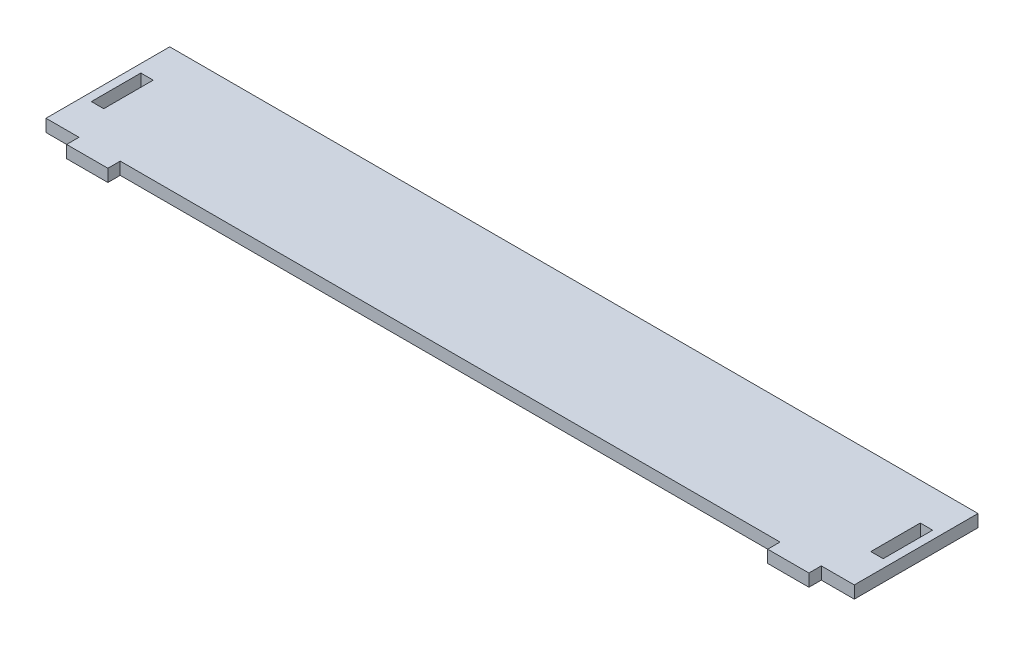
SolidWorks part; units mm, degrees
ref_plane "前视基准面" through (0, 0, 0) normal (0, 0, 1) x (1, 0, 0)
ref_plane "上视基准面" through (0, 0, 0) normal (0, 1, 0) x (1, 0, 0)
ref_plane "右视基准面" through (0, 0, 0) normal (1, 0, 0) x (0, 0, -1)
sketch "草图1" plane through (0, 0, 0) normal (0, 1, 0) x (1, 0, 0)
  line L0 (180, 30) -> (183, 30)
  line L1 (10, 0) -> (170, 0)
  line L3 (0, 30) -> (180, 30)
  line L6 (0, 0) -> (0, -3)
  line L7 (0, -3) -> (10, -3)
  line L8 (10, 0) -> (10, -3)
  line L10 (180, 0) -> (180, -3)
  line L11 (180, -3) -> (170, -3)
  line L12 (170, 0) -> (170, -3)
  line L13 (183, 21) -> (183, 9)
  line L14 (183, 0) -> (180, 0)
  line L15 (183, 9) -> (183, 21)
  line L16 (183, 21) -> (186, 21)
  line L17 (186, 21) -> (186, 9)
  line L18 (186, 9) -> (183, 9)
  line L19 (183, 30) -> (188, 30)
  line L20 (188, 30) -> (188, 0)
  line L21 (188, 0) -> (183, 0)
  line L22 (-3, 9) -> (-3, 21)
  line L23 (0, 30) -> (-3, 30)
  line L25 (0, 0) -> (-3, 0)
  line L26 (-3, 21) -> (-3, 9)
  line L27 (-3, 21) -> (-6, 21)
  line L28 (-6, 21) -> (-6, 9)
  line L29 (-6, 9) -> (-3, 9)
  line L30 (-3, 30) -> (-8, 30)
  line L31 (-8, 30) -> (-8, 0)
  line L32 (-8, 0) -> (-3, 0)
  point P16 (183, 15)
  point P26 (-3, 15)
extrude "凸台-拉伸1" add sketch "草图1" along normal blind 3 contours L31 L32 L25 L6 L7 L8 L1 L12 L11 L10 L14 L21 L20 L19 L0 L3 L23 L30 L17 L18 L13 L16 L29 L28 L27 L22
